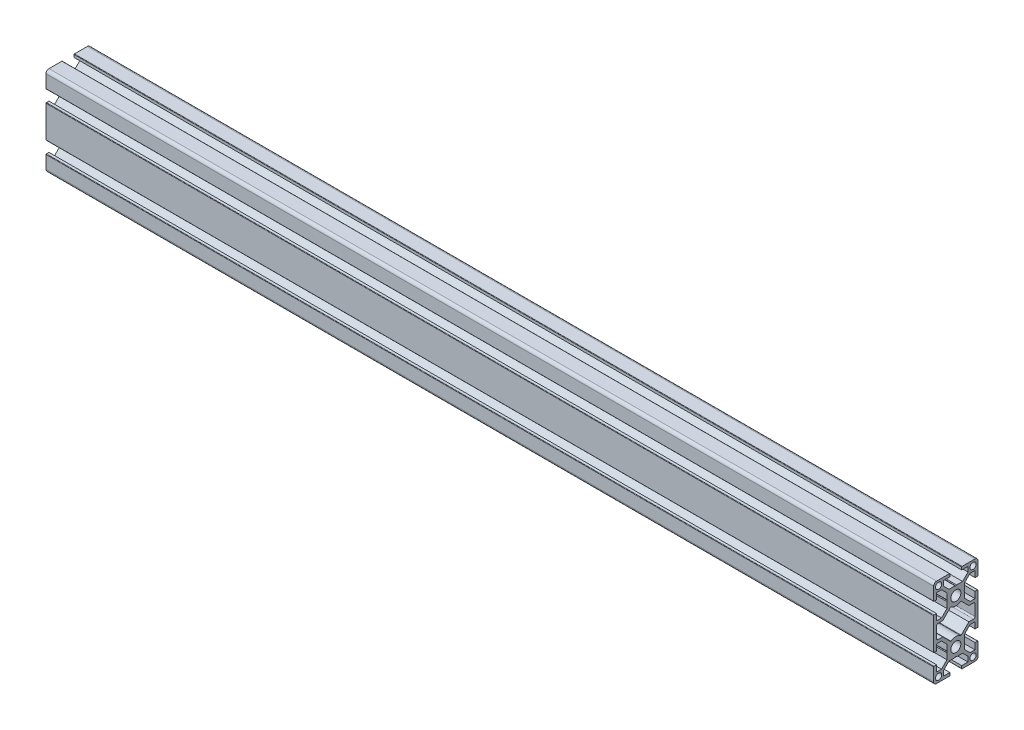
SolidWorks part; units mm, degrees
ref_plane "Front Plane" through (0, 0, 0) normal (0, 0, 1) x (1, 0, 0)
ref_plane "Top Plane" through (0, 0, 0) normal (0, 1, 0) x (1, 0, 0)
ref_plane "Right Plane" through (0, 0, 0) normal (1, 0, 0) x (0, 0, -1)
sketch "Sketch1" plane through (0, 0, 0) normal (0, 1, 0) x (1, 0, 0)
  line L0 (0, 0) -> (-600, 0)
  dimension "D1" = 600
other "30xs6 30X60S6(1)"
ref_plane "Plane1" through (0, 0, 0) normal (-1, 0, 0) x (0, 0, 1)
sketch "草图1" plane through (0, 0, 0) normal (-1, 0, 0) x (0, 0, 1)
  line L0 (-13, -30) -> (-4.3, -30)
  line L1 (-4, -29.7) -> (-4, -28)
  line L2 (-4, -28) -> (-8.25, -28)
  line L3 (-8.25, -28) -> (-8.25, -24.6642)
  line L4 (-8.25, -24.6642) -> (-4.5858, -21)
  line L5 (-4.5858, -21) -> (-0.5196, -21)
  line L6 (-0.5196, -21) -> (0, -20.7)
  line L7 (0, -20.7) -> (0.5196, -21)
  line L8 (0.5196, -21) -> (4.5858, -21)
  line L9 (4.5858, -21) -> (8.25, -24.6642)
  line L10 (8.25, -24.6642) -> (8.25, -28)
  line L11 (8.25, -28) -> (4, -28)
  line L12 (4, -28) -> (4, -29.7)
  line L13 (4.3, -30) -> (13, -30)
  line L14 (15, -28) -> (15, -19.3)
  line L15 (14.7, -19) -> (13, -19)
  line L16 (13, -19) -> (13, -23.25)
  line L17 (13, -23.25) -> (9.6642, -23.25)
  line L18 (9.6642, -23.25) -> (6, -19.5858)
  line L19 (6, -19.5858) -> (6, -15.5196)
  line L20 (6, -15.5196) -> (5.7, -15)
  line L21 (5.7, -15) -> (6, -14.4804)
  line L22 (6, -14.4804) -> (6, -10.4142)
  line L23 (6, -10.4142) -> (9.6642, -6.75)
  line L24 (9.6642, -6.75) -> (13, -6.75)
  line L25 (13, -6.75) -> (13, -11)
  line L26 (13, -11) -> (14.7, -11)
  line L27 (15, -10.7) -> (15, 10.7)
  line L28 (14.7, 11) -> (13, 11)
  line L29 (13, 11) -> (13, 6.75)
  line L30 (13, 6.75) -> (9.6642, 6.75)
  line L31 (9.6642, 6.75) -> (6, 10.4142)
  line L32 (6, 10.4142) -> (6, 14.4804)
  line L33 (6, 14.4804) -> (5.7, 15)
  line L34 (5.7, 15) -> (6, 15.5196)
  line L35 (6, 15.5196) -> (6, 19.5858)
  line L36 (6, 19.5858) -> (9.6642, 23.25)
  line L37 (9.6642, 23.25) -> (13, 23.25)
  line L38 (13, 23.25) -> (13, 19)
  line L39 (13, 19) -> (14.7, 19)
  line L40 (15, 19.3) -> (15, 28)
  line L41 (13, 30) -> (4.3, 30)
  line L42 (4, 29.7) -> (4, 28)
  line L43 (4, 28) -> (8.25, 28)
  line L44 (8.25, 28) -> (8.25, 24.6642)
  line L45 (8.25, 24.6642) -> (4.5858, 21)
  line L46 (4.5858, 21) -> (0.5196, 21)
  line L47 (0.5196, 21) -> (0, 20.7)
  line L48 (0, 20.7) -> (-0.5196, 21)
  line L49 (-0.5196, 21) -> (-4.5858, 21)
  line L50 (-4.5858, 21) -> (-8.25, 24.6642)
  line L51 (-8.25, 24.6642) -> (-8.25, 28)
  line L52 (-8.25, 28) -> (-4, 28)
  line L53 (-4, 28) -> (-4, 29.7)
  line L54 (-4.3, 30) -> (-13, 30)
  line L55 (-15, 28) -> (-15, 19.3)
  line L56 (-14.7, 19) -> (-13, 19)
  line L57 (-13, 19) -> (-13, 23.25)
  line L58 (-13, 23.25) -> (-9.6642, 23.25)
  line L59 (-9.6642, 23.25) -> (-6, 19.5858)
  line L60 (-6, 19.5858) -> (-6, 15.5196)
  line L61 (-6, 15.5196) -> (-5.7, 15)
  line L62 (-5.7, 15) -> (-6, 14.4804)
  line L63 (-6, 14.4804) -> (-6, 10.4142)
  line L64 (-6, 10.4142) -> (-9.6642, 6.75)
  line L65 (-9.6642, 6.75) -> (-13, 6.75)
  line L66 (-13, 6.75) -> (-13, 11)
  line L67 (-13, 11) -> (-14.7, 11)
  line L68 (-15, 10.7) -> (-15, -10.7)
  line L69 (-14.7, -11) -> (-13, -11)
  line L70 (-13, -11) -> (-13, -6.75)
  line L71 (-13, -6.75) -> (-9.6642, -6.75)
  line L72 (-9.6642, -6.75) -> (-6, -10.4142)
  line L73 (-6, -10.4142) -> (-6, -14.4804)
  line L74 (-6, -14.4804) -> (-5.7, -15)
  line L75 (-5.7, -15) -> (-6, -15.5196)
  line L76 (-6, -15.5196) -> (-6, -19.5858)
  line L77 (-6, -19.5858) -> (-9.6642, -23.25)
  line L78 (-9.6642, -23.25) -> (-13, -23.25)
  line L79 (-13, -23.25) -> (-13, -19)
  line L80 (-13, -19) -> (-14.7, -19)
  line L81 (-15, -19.3) -> (-15, -28)
  line L82 (-13, 3.75) -> (-13, -3.75)
  line L83 (-12, -4.75) -> (-8.8358, -4.75)
  line L84 (-8.8358, -4.75) -> (-3.6518, -9.934)
  line L85 (3.6518, -9.934) -> (8.8358, -4.75)
  line L86 (8.8358, -4.75) -> (12, -4.75)
  line L87 (13, -3.75) -> (13, 3.75)
  line L88 (12, 4.75) -> (8.8358, 4.75)
  line L89 (8.8358, 4.75) -> (3.6518, 9.934)
  line L90 (-3.6518, 9.934) -> (-8.8358, 4.75)
  line L91 (-8.8358, 4.75) -> (-12, 4.75)
  arc A0 (-15, -28) -> (-13, -30) centre (-13, -28) ccw
  arc A1 (-4.3, -30) -> (-4, -29.7) centre (-4.3, -29.7) ccw
  arc A2 (4, -29.7) -> (4.3, -30) centre (4.3, -29.7) ccw
  arc A3 (13, -30) -> (15, -28) centre (13, -28) ccw
  arc A4 (15, -19.3) -> (14.7, -19) centre (14.7, -19.3) ccw
  arc A5 (14.7, -11) -> (15, -10.7) centre (14.7, -10.7) ccw
  arc A6 (15, 10.7) -> (14.7, 11) centre (14.7, 10.7) ccw
  arc A7 (14.7, 19) -> (15, 19.3) centre (14.7, 19.3) ccw
  arc A8 (15, 28) -> (13, 30) centre (13, 28) ccw
  arc A9 (4.3, 30) -> (4, 29.7) centre (4.3, 29.7) ccw
  arc A10 (-4, 29.7) -> (-4.3, 30) centre (-4.3, 29.7) ccw
  arc A11 (-13, 30) -> (-15, 28) centre (-13, 28) ccw
  arc A12 (-15, 19.3) -> (-14.7, 19) centre (-14.7, 19.3) ccw
  arc A13 (-14.7, 11) -> (-15, 10.7) centre (-14.7, 10.7) ccw
  arc A14 (-15, -10.7) -> (-14.7, -11) centre (-14.7, -10.7) ccw
  arc A15 (-14.7, -19) -> (-15, -19.3) centre (-14.7, -19.3) ccw
  circle A16 centre (11.625, 26.625) radius 2.1
  circle A17 centre (11.625, -26.625) radius 2.1
  circle A18 centre (0, -15) radius 3.4
  circle A19 centre (0, 15) radius 3.4
  arc A20 (-13, -3.75) -> (-12, -4.75) centre (-12, -3.75) ccw
  arc A21 (-3.6518, -9.934) -> (-3.2759, -9.9732) centre (-3.4397, -9.7219) ccw
  arc A22 (-3.2759, -9.9732) -> (3.2759, -9.9732) centre (0, -15) cw
  arc A23 (3.2759, -9.9732) -> (3.6518, -9.934) centre (3.4397, -9.7219) ccw
  arc A24 (12, -4.75) -> (13, -3.75) centre (12, -3.75) ccw
  arc A25 (13, 3.75) -> (12, 4.75) centre (12, 3.75) ccw
  arc A26 (3.6518, 9.934) -> (3.2759, 9.9732) centre (3.4397, 9.7219) ccw
  arc A27 (3.2759, 9.9732) -> (-3.2759, 9.9732) centre (0, 15) cw
  arc A28 (-3.2759, 9.9732) -> (-3.6518, 9.934) centre (-3.4397, 9.7219) ccw
  arc A29 (-12, 4.75) -> (-13, 3.75) centre (-12, 3.75) ccw
  circle A30 centre (-11.625, 26.625) radius 2.1
  circle A31 centre (-11.625, -26.625) radius 2.1
  point P154 (-15, 30)
  point P155 (0, 30)
  point P156 (15, 30)
  point P157 (15, 15)
  point P158 (-15, 15)
  point P159 (-15, 0)
  point P160 (15, 0)
  point P161 (15, -15)
  point P162 (-15, -15)
  point P163 (15, -30)
  point P164 (-15, -30)
  point P165 (0, -30)
  point P166 (0, 0)
